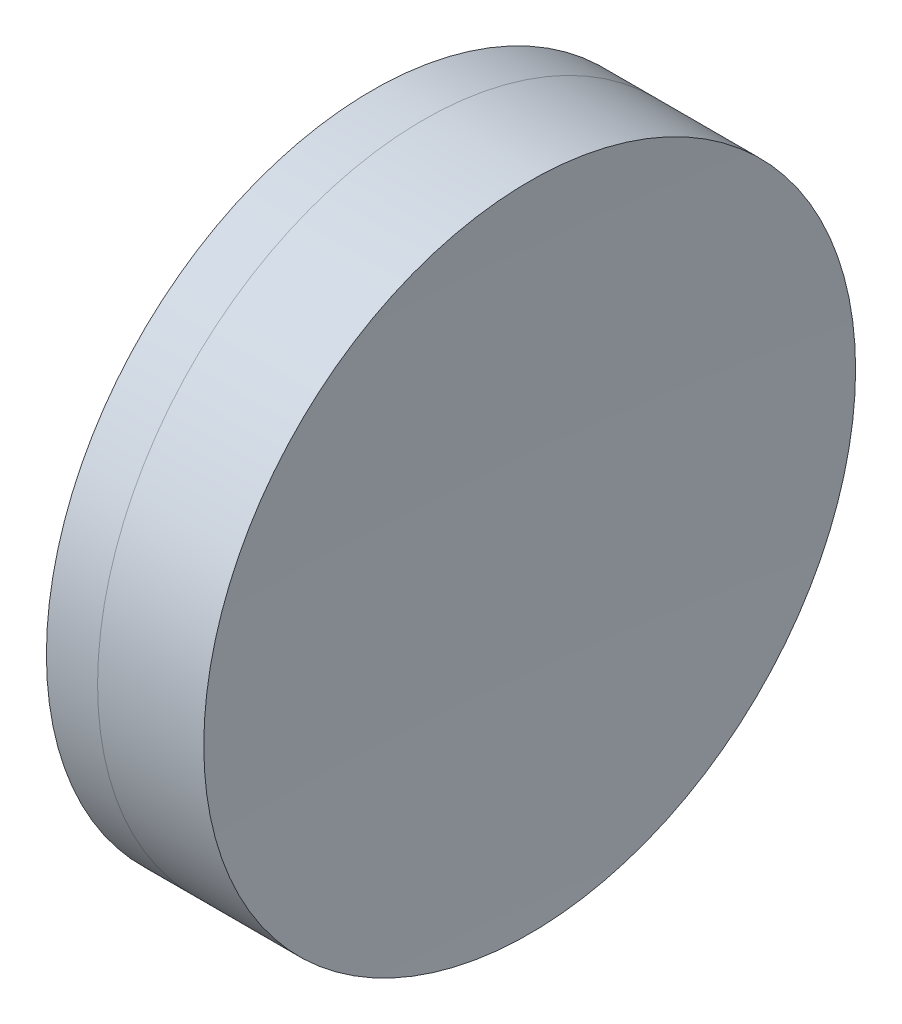
SolidWorks part; units mm, degrees
ref_plane "前视基准面" through (0, 0, 0) normal (0, 0, 1) x (1, 0, 0)
ref_plane "上视基准面" through (0, 0, 0) normal (0, 1, 0) x (1, 0, 0)
ref_plane "右视基准面" through (0, 0, 0) normal (1, 0, 0) x (0, 0, -1)
sketch "草图1" plane through (0, 0, 0) normal (0, 1, 0) x (1, 0, 0)
  line L0 (-0.8161, 0) -> (118.0272, 0) construction
  line L1 (95.8259, -12.7) -> (97.8199, -12.7)
  line L2 (95.8259, 12.7) -> (97.8199, 12.7)
  arc A0 (97.8199, -12.7) -> (97.8199, 12.7) centre (2.7242, 0) ccw
  arc A1 (95.8259, 12.7) -> (95.8259, -12.7) centre (164.6642, 0) ccw
  point P4 (118.0272, 0)
  point P10 (94.6642, 0)
  point P11 (98.6642, 0)
  dimension "D3" = 70
  dimension "D4" = 95.94
  dimension "D1" = 12.7
  dimension "D2" = 12.7
  dimension "D5" = 4
revolve "旋转1" add sketch "草图1" angle 360 about L0
sketch "草图2" plane through (0, 0, 0) normal (0, 1, 0) x (1, 0, 0)
  line L0 (-0.5519, 0) -> (162.8134, 0) construction
  line L2 (97.8199, 12.7) -> (101.9583, 12.7)
  line L3 (97.8199, -12.7) -> (101.9583, -12.7)
  arc A0 (101.9583, 12.7) -> (101.9583, -12.7) centre (375.9742, 0) ccw
  arc A1 (97.8199, -12.7) -> (97.8199, 12.7) centre (2.7242, 0) ccw construction
  arc A2 (97.8199, -12.7) -> (97.8199, 12.7) centre (2.7242, 0) ccw
  point P4 (98.6642, 0)
  point P8 (101.6642, 0)
  point P9 (162.8134, 0)
  dimension "D1" = 274.31
  dimension "D2" = 3
revolve "旋转2" add sketch "草图2" angle 360 about L0
